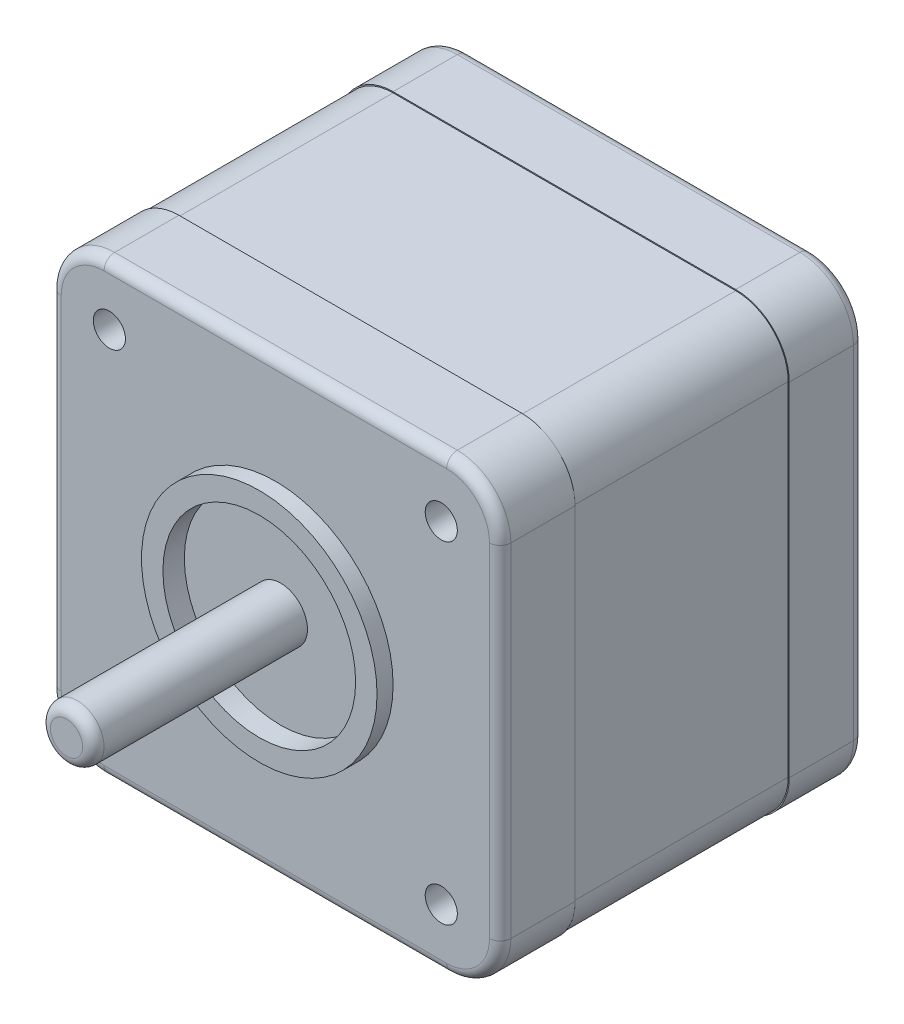
SolidWorks part; units mm, degrees
ref_plane "Front Plane" through (0, 0, 0) normal (0, 0, 1) x (1, 0, 0)
ref_plane "Top Plane" through (0, 0, 0) normal (0, 1, 0) x (1, 0, 0)
ref_plane "Right Plane" through (0, 0, 0) normal (1, 0, 0) x (0, 0, -1)
sketch "Sketch2" plane through (0, 0, 0) normal (0, 0, 1) x (1, 0, 0)
  line L1 (-16, -21) -> (16, -21)
  line L2 (-21, -16) -> (-21, 16)
  line L3 (-16, 21) -> (16, 21)
  line L4 (21, -16) -> (21, 16)
  line L5 (-21, -21) -> (21, 21) construction
  line L6 (-21, 21) -> (21, -21) construction
  arc A0 (16, 21) -> (21, 16) centre (16, 16) cw
  arc A1 (16, -21) -> (21, -16) centre (16, -16) ccw
  arc A2 (-16, -21) -> (-21, -16) centre (-16, -16) cw
  arc A3 (-21, 16) -> (-16, 21) centre (-16, 16) cw
  point P0 (0, 0)
  dimension "D2" = 5
  dimension "D1" = 42
extrude "Boss-Extrude1" add sketch "Sketch2" along normal blind 34
sketch "Sketch4" plane through (0, 0, 34) normal (0, 0, 1) x (1, 0, 0)
  circle A0 centre (0, 0) radius 11
  dimension "D1" = 22
extrude "Boss-Extrude2" add sketch "Sketch4" along normal blind 1.5
sketch "Sketch5" plane through (0, -21, 0) normal (0, -1, 0) x (1, 0, 0)
  line L1 (-7.5, 10) -> (7.5, 10)
  line L2 (-7.5, 10) -> (-7.5, 4)
  line L3 (-7.5, 4) -> (7.5, 4)
  line L4 (7.5, 10) -> (7.5, 4)
  line L5 (-7.5, 10) -> (7.5, 4) construction
  line L6 (-7.5, 4) -> (7.5, 10) construction
  line L7 (0, 7) -> (0, 0) construction
  line L8 (-16, 0) -> (16, 0) construction
  point P0 (0, 7)
  dimension "D1" = 15
  dimension "D2" = 6
  dimension "D3" = 4
extrude "Boss-Extrude3" add sketch "Sketch5" along normal blind 6
sketch "Sketch6" plane through (0, 0, 35.5) normal (0, 0, 1) x (1, 0, 0)
  circle A2 centre (0, 0) radius 9
  circle A3 centre (0, 0) radius 9
  dimension "D1" = 2
extrude "Cut-Extrude1" cut sketch "Sketch6" against normal blind 2
sketch "Sketch7" plane through (0, 0, 33.5) normal (0, 0, 1) x (1, 0, 0)
  circle A0 centre (0, 0) radius 2.5
  dimension "D1" = 5
extrude "Boss-Extrude4" add sketch "Sketch7" along normal blind 20
ref_plane "Plane1" through (0, 0, 27) normal (0, 0, 1) x (1, 0, 0)
sketch "Sketch8" plane through (0, 0, 27) normal (0, 0, 1) x (1, 0, 0)
  line L8 (16, 20.9) -> (-16, 20.9)
  line L9 (-20.9, 16) -> (-20.9, -16)
  line L10 (-16, -20.9) -> (16, -20.9)
  line L11 (20.9, -16) -> (20.9, 16)
  line L12 (16, 20.9) -> (-16, 20.9)
  line L13 (-20.9, 16) -> (-20.9, -16)
  line L14 (-16, -20.9) -> (16, -20.9)
  line L15 (20.9, -16) -> (20.9, 16)
  line L16 (16, 21) -> (-16, 21)
  line L17 (-21, 16) -> (-21, -16)
  line L18 (-16, -21) -> (16, -21)
  line L19 (21, -16) -> (21, 16)
  line L20 (16, 21) -> (-16, 21)
  line L21 (-21, 16) -> (-21, -16)
  line L22 (-16, -21) -> (16, -21)
  line L23 (21, -16) -> (21, 16)
  arc A8 (20.9, 16) -> (16, 20.9) centre (16, 16) ccw
  arc A9 (-16, 20.9) -> (-20.9, 16) centre (-16, 16) ccw
  arc A10 (-20.9, -16) -> (-16, -20.9) centre (-16, -16) ccw
  arc A11 (16, -20.9) -> (20.9, -16) centre (16, -16) ccw
  arc A12 (20.9, 16) -> (16, 20.9) centre (16, 16) ccw
  arc A13 (-16, 20.9) -> (-20.9, 16) centre (-16, 16) ccw
  arc A14 (-20.9, -16) -> (-16, -20.9) centre (-16, -16) ccw
  arc A15 (16, -20.9) -> (20.9, -16) centre (16, -16) ccw
  arc A16 (21, 16) -> (16, 21) centre (16, 16) ccw
  arc A17 (-16, 21) -> (-21, 16) centre (-16, 16) ccw
  arc A18 (-21, -16) -> (-16, -21) centre (-16, -16) ccw
  arc A19 (16, -21) -> (21, -16) centre (16, -16) ccw
  arc A20 (21, 16) -> (16, 21) centre (16, 16) ccw
  arc A21 (-16, 21) -> (-21, 16) centre (-16, 16) ccw
  arc A22 (-21, -16) -> (-16, -21) centre (-16, -16) ccw
  arc A23 (16, -21) -> (21, -16) centre (16, -16) ccw
  dimension "D1" = 0.1
  dimension "D2" = 0
extrude "Cut-Extrude3" cut sketch "Sketch8" against normal blind 20
fillet "Fillet1" radius 1 16 edges at (19.5355, 19.5355, 0) (21, 0, 0) (19.5355, -19.5355, 0) (0, -21, 0) (-19.5355, -19.5355, 0) (-21, 0, 0) (-19.5355, 19.5355, 0) (-19.5355, 19.5355, 34) (0, 21, 34) (19.5355, 19.5355, 34) (21, 0, 34) (19.5355, -19.5355, 34) (0, -21, 34) (-19.5355, -19.5355, 34) (0, 21, 0) (-21, 0, 34)
fillet "Fillet2" radius 1 1 edges at (2.5, 0, 53.5)
sketch "Sketch9" plane through (0, 0, 34) normal (0, 0, 1) x (1, 0, 0)
  line L1 (-15.5, 15.5) -> (15.5, 15.5) construction
  line L2 (-15.5, 15.5) -> (-15.5, -15.5) construction
  line L3 (-15.5, -15.5) -> (15.5, -15.5) construction
  line L4 (15.5, 15.5) -> (15.5, -15.5) construction
  line L5 (-15.5, 15.5) -> (15.5, -15.5) construction
  line L6 (-15.5, -15.5) -> (15.5, 15.5) construction
  circle A0 centre (15.5, 15.5) radius 1.5
  circle A1 centre (15.5, -15.5) radius 1.5
  circle A2 centre (-15.5, -15.5) radius 1.5
  circle A3 centre (-15.5, 15.5) radius 1.5
  point P0 (0, 0)
  dimension "D2" = 3
  dimension "D1" = 31
extrude "Cut-Extrude4" cut sketch "Sketch9" against normal blind 20
